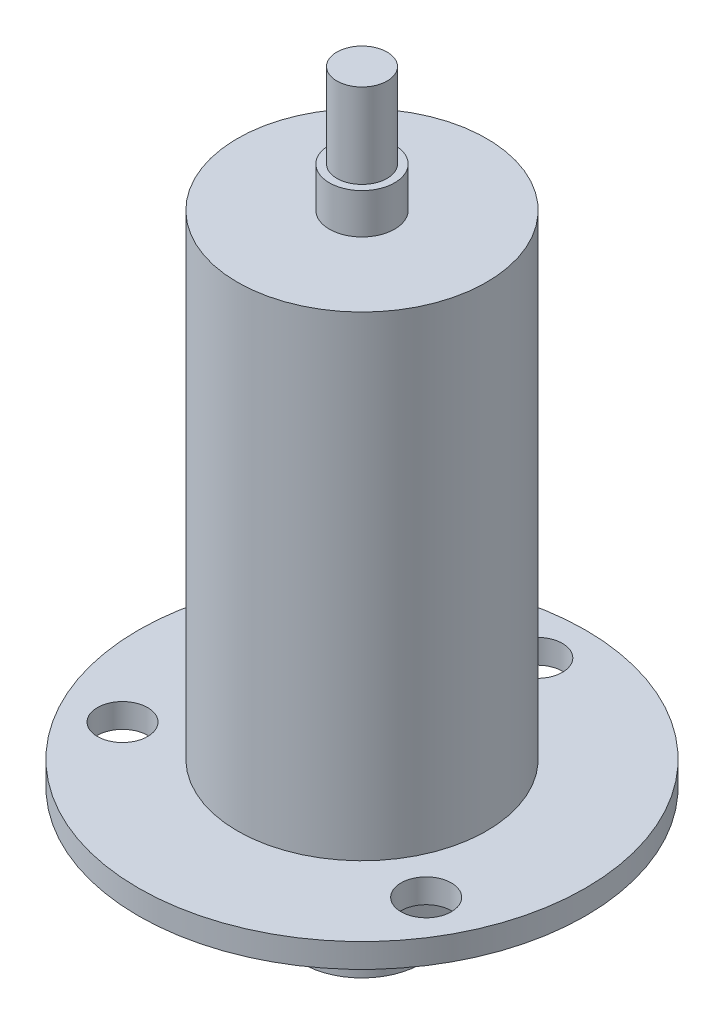
SolidWorks part; units mm, degrees
ref_plane "Front Plane" through (0, 0, 0) normal (0, 0, 1) x (1, 0, 0)
ref_plane "Top Plane" through (0, 0, 0) normal (0, 1, 0) x (1, 0, 0)
ref_plane "Right Plane" through (0, 0, 0) normal (1, 0, 0) x (0, 0, -1)
sketch "Sketch2" plane through (0, 0, 0) normal (0, 1, 0) x (1, 0, 0)
  line L0 (0, 17.45) -> (0, -0.3236) construction
  circle A0 centre (0, 0) radius 22.25
  circle A1 centre (0, 0) radius 17.45 construction
  circle A2 centre (0, 17.45) radius 2.5
  circle A3 centre (15.1121, -8.725) radius 2.5
  circle A4 centre (-15.1121, -8.725) radius 2.5
  point P14 (0, 0)
  dimension "D1" = 44.5
  dimension "D2" = 34.9
  dimension "D3" = 5
  dimension "D4" = 3
extrude "Boss-Extrude1" add sketch "Sketch2" along normal blind 2.4
sketch "Sketch3" plane through (0, 2.4, 0) normal (0, 1, 0) x (1, 0, 0)
  circle A0 centre (0, 0) radius 12.4
  dimension "D1" = 24.8
extrude "Boss-Extrude2" add sketch "Sketch3" along normal blind 47.3
sketch "Sketch4" plane through (0, 49.7, 0) normal (0, 1, 0) x (1, 0, 0)
  circle A0 centre (0, 0) radius 3.25
  dimension "D1" = 6.5
extrude "Boss-Extrude3" add sketch "Sketch4" along normal blind 4
sketch "Sketch5" plane through (0, 53.7, 0) normal (0, 1, 0) x (1, 0, 0)
  circle A0 centre (0, 0) radius 2.5
  dimension "D1" = 5
extrude "Boss-Extrude4" add sketch "Sketch5" along normal blind 8.4
sketch "Sketch6" plane through (0, 0, 0) normal (0, -1, 0) x (1, 0, 0)
  circle A0 centre (0, 0) radius 12.385
  dimension "D1" = 24.77
extrude "Boss-Extrude5" add sketch "Sketch6" along normal blind 5.1
sketch "Sketch7" plane through (0, -5.1, 0) normal (0, -1, 0) x (1, 0, 0)
  circle A0 centre (0, 0) radius 5.9
  dimension "D1" = 11.8
extrude "Boss-Extrude6" add sketch "Sketch7" along normal blind 7.2
